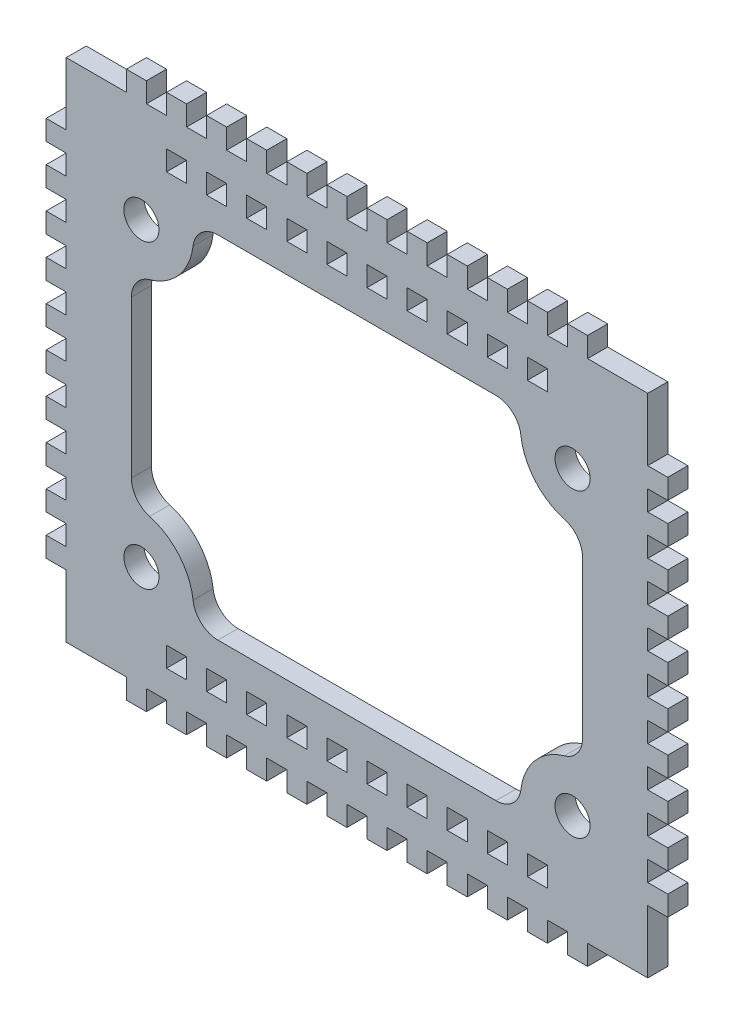
SolidWorks part; units mm, degrees
material "Cedar"
ref_plane "Front Plane" through (0, 0, 0) normal (0, 0, 1) x (1, 0, 0)
ref_plane "Top Plane" through (0, 0, 0) normal (0, 1, 0) x (1, 0, 0)
ref_plane "Right Plane" through (0, 0, 0) normal (1, 0, 0) x (0, 0, -1)
sketch "Sketch1" plane through (0, 0, 0) normal (0, 0, 1) x (1, 0, 0)
  line L0 (0, 0) -> (0, 50) construction
  line L1 (0, 0) -> (-64, 0) construction
  line L2 (-58, -50.5) -> (-58, 50.5)
  line L3 (-58, 50.5) -> (58, 50.5)
  line L4 (-45, -20) -> (-45, 20)
  line L5 (-33, 35) -> (33, 35)
  line L6 (45, -20) -> (45, 20)
  line L7 (58, -50.5) -> (58, 50.5)
  line L8 (-58, -50.5) -> (58, -50.5)
  line L9 (-33, -35) -> (33, -35)
  circle A0 centre (-43, 30) radius 3.5
  arc A1 (-45, 20) -> (-33, 35) centre (-44.6174, 31.9939) ccw
  arc A2 (45, -20) -> (33, -35) centre (44.6174, -31.9939) ccw
  circle A3 centre (43, 30) radius 3.5
  circle A4 centre (43, -30) radius 3.5
  circle A5 centre (-43, -30) radius 3.5
  arc A6 (45, 20) -> (33, 35) centre (44.6174, 31.9939) cw
  arc A7 (-45, -20) -> (-33, -35) centre (-44.6174, -31.9939) cw
  point P19 (0, 35)
  point P21 (0, 50.5)
  point P27 (-64, 0)
  point P28 (64, 0)
  point P29 (45, 0)
  point P34 (-45, 0)
  dimension "D3" = 7
  dimension "D8" = 50.5
  dimension "D7" = 10
  dimension "D9" = 35
  dimension "D10" = 12
  dimension "D11" = 50.5
  dimension "D1" = 10
  dimension "D2" = 116
  dimension "D4" = 43
  dimension "D5" = 45
  dimension "D6" = 30
extrude "Boss-Extrude1" add sketch "Sketch1" along normal blind 4
sketch "Sketch3" plane through (0, 0, 4) normal (0, 0, 1) x (1, 0, 0)
  line L0 (0, 0) -> (0, 54.6046) construction
  line L3 (-58, 50.5) -> (58, 50.5) construction
  line L6 (-14, 40.75) -> (-14, 44.75)
  line L7 (-10, 44.75) -> (-14, 44.75)
  line L8 (-10, 40.75) -> (-10, 44.75)
  line L9 (-10, 40.75) -> (-14, 40.75)
  line L10 (-22, 40.75) -> (-22, 44.75)
  line L12 (-18, 44.75) -> (-22, 44.75)
  line L13 (-18, 40.75) -> (-18, 44.75)
  line L14 (-18, 40.75) -> (-22, 40.75)
  line L15 (0, 0) -> (-26.3378, 0) construction
  line L16 (0, 0) -> (-64, 0) construction
  line L17 (-30, 40.75) -> (-30, 44.75)
  line L18 (-26, 44.75) -> (-30, 44.75)
  line L19 (-26, 40.75) -> (-26, 44.75)
  line L20 (-26, 40.75) -> (-30, 40.75)
  line L21 (33, -35) -> (33, -50.5) construction
  line L22 (-58, -50.5) -> (58, -50.5) construction
  line L24 (-14, -41) -> (-10, -41)
  line L25 (-6, -41) -> (-2, -41)
  line L26 (-6, -41) -> (-6, -45)
  line L27 (-6, -45) -> (-2, -45)
  line L28 (-2, -41) -> (-2, -45)
  line L29 (-38, 40.75) -> (-38, 44.75)
  line L30 (-34, 44.75) -> (-38, 44.75)
  line L31 (-34, 40.75) -> (-34, 44.75)
  line L32 (-34, 40.75) -> (-38, 40.75)
  line L33 (2, 40.75) -> (6, 40.75)
  line L35 (2, 40.75) -> (2, 44.75)
  line L36 (2, 44.75) -> (6, 44.75)
  line L37 (6, 40.75) -> (6, 44.75)
  line L39 (34, 40.75) -> (38, 40.75)
  line L40 (34, 40.75) -> (34, 44.75)
  line L41 (34, 44.75) -> (38, 44.75)
  line L42 (38, 40.75) -> (38, 44.75)
  line L43 (26, 40.75) -> (30, 40.75)
  line L44 (26, 40.75) -> (26, 44.75)
  line L45 (26, 44.75) -> (30, 44.75)
  line L46 (30, 40.75) -> (30, 44.75)
  line L47 (18, 40.75) -> (22, 40.75)
  line L48 (18, 40.75) -> (18, 44.75)
  line L49 (18, 44.75) -> (22, 44.75)
  line L50 (22, 40.75) -> (22, 44.75)
  line L51 (10, 40.75) -> (14, 40.75)
  line L52 (10, 40.75) -> (10, 44.75)
  line L53 (10, 44.75) -> (14, 44.75)
  line L54 (14, 40.75) -> (14, 44.75)
  line L55 (-14, -41) -> (-14, -45)
  line L56 (-14, -45) -> (-10, -45)
  line L57 (-10, -41) -> (-10, -45)
  line L58 (-6, 40.75) -> (-6, 44.75)
  line L59 (-2, 44.75) -> (-6, 44.75)
  line L60 (-2, 40.75) -> (-2, 44.75)
  line L61 (-2, 40.75) -> (-6, 40.75)
  line L62 (-22, -41) -> (-18, -41)
  line L63 (-22, -41) -> (-22, -45)
  line L64 (-22, -45) -> (-18, -45)
  line L65 (-18, -41) -> (-18, -45)
  line L66 (-30, -41) -> (-26, -41)
  line L67 (-30, -41) -> (-30, -45)
  line L68 (-30, -45) -> (-26, -45)
  line L69 (-26, -41) -> (-26, -45)
  line L70 (-38, -41) -> (-34, -41)
  line L71 (-38, -41) -> (-38, -45)
  line L72 (-38, -45) -> (-34, -45)
  line L73 (-34, -41) -> (-34, -45)
  line L74 (34, -41) -> (34, -45)
  line L75 (38, -45) -> (34, -45)
  line L76 (38, -41) -> (38, -45)
  line L77 (38, -41) -> (34, -41)
  line L78 (26, -41) -> (26, -45)
  line L79 (30, -45) -> (26, -45)
  line L80 (30, -41) -> (30, -45)
  line L81 (30, -41) -> (26, -41)
  line L82 (18, -41) -> (18, -45)
  line L83 (22, -45) -> (18, -45)
  line L84 (22, -41) -> (22, -45)
  line L85 (22, -41) -> (18, -41)
  line L86 (10, -41) -> (10, -45)
  line L87 (14, -45) -> (10, -45)
  line L88 (14, -41) -> (14, -45)
  line L89 (2, -41) -> (2, -45)
  line L90 (6, -45) -> (2, -45)
  line L91 (6, -41) -> (6, -45)
  line L92 (6, -41) -> (2, -41)
  line L93 (14, -41) -> (10, -41)
  dimension "D1" = 5.75
  dimension "D2" = 4
  dimension "D3" = 4
  dimension "D4" = 4
  dimension "D6" = 2
  dimension "D7" = 5
  dimension "D8" = 5.5
  dimension "D9" = 5
  dimension "D5" = 4
  dimension "D10" = 2
extrude "Cut-Extrude2" cut sketch "Sketch3" against normal blind 4
fillet "Fillet1" radius 5 1 edges at (-45, 20, 2)
fillet "Fillet2" radius 5 1 edges at (-33, 35, 2)
fillet "Fillet3" radius 5 1 edges at (33, 35, 2)
fillet "Fillet4" radius 5 1 edges at (45, 20, 2)
fillet "Fillet5" radius 5 1 edges at (33, -35, 2)
fillet "Fillet6" radius 5 1 edges at (45, -20, 2)
fillet "Fillet7" radius 5 1 edges at (-45, -20, 2)
fillet "Fillet8" radius 5 1 edges at (-33, -35, 2)
sketch "Sketch4" plane through (0, 0, 4) normal (0, 0, 1) x (1, 0, 0)
  line L0 (-58, -50.5) -> (-58, 50.5) construction
  line L1 (-58, 6) -> (-62, 6)
  line L2 (-58, 6) -> (-58, 2)
  line L3 (-58, 2) -> (-62, 2)
  line L4 (-62, 6) -> (-62, 2)
  line L5 (0, 0) -> (-64, 0) construction
  line L6 (-58, 14) -> (-62, 14)
  line L7 (-58, 14) -> (-58, 10)
  line L8 (-58, 10) -> (-62, 10)
  line L9 (-62, 14) -> (-62, 10)
  line L10 (-58, 22) -> (-62, 22)
  line L11 (-58, 22) -> (-58, 18)
  line L12 (-58, 18) -> (-62, 18)
  line L13 (-62, 22) -> (-62, 18)
  line L14 (-58, 30) -> (-62, 30)
  line L15 (-58, 30) -> (-58, 26)
  line L16 (-58, 26) -> (-62, 26)
  line L17 (-62, 30) -> (-62, 26)
  line L18 (-58, 38) -> (-62, 38)
  line L19 (-58, 38) -> (-58, 34)
  line L20 (-58, 34) -> (-62, 34)
  line L21 (-62, 38) -> (-62, 34)
  line L22 (0, 0) -> (-100.6812, 0) construction
  line L23 (-62, -38) -> (-62, -34)
  line L24 (-58, -34) -> (-62, -34)
  line L25 (-58, -38) -> (-58, -34)
  line L26 (-58, -38) -> (-62, -38)
  line L27 (-62, -30) -> (-62, -26)
  line L28 (-58, -26) -> (-62, -26)
  line L29 (-58, -30) -> (-58, -26)
  line L30 (-58, -30) -> (-62, -30)
  line L31 (-62, -22) -> (-62, -18)
  line L32 (-58, -18) -> (-62, -18)
  line L33 (-58, -22) -> (-58, -18)
  line L34 (-58, -22) -> (-62, -22)
  line L35 (-62, -14) -> (-62, -10)
  line L36 (-58, -10) -> (-62, -10)
  line L37 (-58, -14) -> (-58, -10)
  line L38 (-58, -14) -> (-62, -14)
  line L39 (-62, -6) -> (-62, -2)
  line L40 (-58, -2) -> (-62, -2)
  line L41 (-58, -6) -> (-58, -2)
  line L42 (-58, -6) -> (-62, -6)
  line L43 (0, 0) -> (0, 62.8153) construction
  line L44 (58, -6) -> (62, -6)
  line L45 (58, -6) -> (58, -2)
  line L46 (58, -2) -> (62, -2)
  line L47 (62, -6) -> (62, -2)
  line L48 (58, -14) -> (62, -14)
  line L49 (58, -14) -> (58, -10)
  line L50 (58, -10) -> (62, -10)
  line L51 (62, -14) -> (62, -10)
  line L52 (58, -22) -> (62, -22)
  line L53 (58, -22) -> (58, -18)
  line L54 (58, -18) -> (62, -18)
  line L55 (62, -22) -> (62, -18)
  line L56 (58, -30) -> (62, -30)
  line L57 (58, -30) -> (58, -26)
  line L58 (58, -26) -> (62, -26)
  line L59 (62, -30) -> (62, -26)
  line L60 (58, -38) -> (62, -38)
  line L61 (58, -38) -> (58, -34)
  line L62 (58, -34) -> (62, -34)
  line L63 (62, -38) -> (62, -34)
  line L64 (62, 38) -> (62, 34)
  line L65 (58, 34) -> (62, 34)
  line L66 (58, 38) -> (58, 34)
  line L67 (58, 38) -> (62, 38)
  line L68 (62, 30) -> (62, 26)
  line L69 (58, 26) -> (62, 26)
  line L70 (58, 30) -> (58, 26)
  line L71 (58, 30) -> (62, 30)
  line L72 (62, 22) -> (62, 18)
  line L73 (58, 18) -> (62, 18)
  line L74 (58, 22) -> (58, 18)
  line L75 (58, 22) -> (62, 22)
  line L76 (62, 14) -> (62, 10)
  line L77 (58, 10) -> (62, 10)
  line L78 (58, 14) -> (58, 10)
  line L79 (58, 14) -> (62, 14)
  line L80 (62, 6) -> (62, 2)
  line L81 (58, 2) -> (62, 2)
  line L82 (58, 6) -> (58, 2)
  line L83 (58, 6) -> (62, 6)
  dimension "D1" = 4
  dimension "D2" = 4
  dimension "D3" = 2
  dimension "D4" = 5
extrude "Boss-Extrude2" add sketch "Sketch4" against normal blind 4
sketch "Sketch5" plane through (0, 0, 0) normal (0, 0, -1) x (-1, 0, 0)
  line L0 (58, 50.5) -> (-58, 50.5) construction
  line L1 (-2, 50.5) -> (-6, 50.5)
  line L2 (-2, 50.5) -> (-2, 54.5)
  line L3 (-2, 54.5) -> (-6, 54.5)
  line L4 (-6, 50.5) -> (-6, 54.5)
  line L5 (0, 0) -> (0, 50) construction
  line L6 (-10, 50.5) -> (-14, 50.5)
  line L7 (-10, 50.5) -> (-10, 54.5)
  line L8 (-10, 54.5) -> (-14, 54.5)
  line L9 (-14, 50.5) -> (-14, 54.5)
  line L10 (-18, 50.5) -> (-22, 50.5)
  line L11 (-18, 50.5) -> (-18, 54.5)
  line L12 (-18, 54.5) -> (-22, 54.5)
  line L13 (-22, 50.5) -> (-22, 54.5)
  line L14 (-26, 50.5) -> (-30, 50.5)
  line L15 (-26, 50.5) -> (-26, 54.5)
  line L16 (-26, 54.5) -> (-30, 54.5)
  line L17 (-30, 50.5) -> (-30, 54.5)
  line L18 (-34, 50.5) -> (-38, 50.5)
  line L19 (-34, 50.5) -> (-34, 54.5)
  line L20 (-34, 54.5) -> (-38, 54.5)
  line L21 (-38, 50.5) -> (-38, 54.5)
  line L22 (-42, 50.5) -> (-46, 50.5)
  line L23 (-42, 50.5) -> (-42, 54.5)
  line L24 (-42, 54.5) -> (-46, 54.5)
  line L25 (-46, 50.5) -> (-46, 54.5)
  line L26 (0, 50) -> (0, 31.2256) construction
  line L27 (46, 50.5) -> (46, 54.5)
  line L28 (42, 54.5) -> (46, 54.5)
  line L29 (42, 50.5) -> (42, 54.5)
  line L30 (42, 50.5) -> (46, 50.5)
  line L31 (38, 50.5) -> (38, 54.5)
  line L32 (34, 54.5) -> (38, 54.5)
  line L33 (34, 50.5) -> (34, 54.5)
  line L34 (34, 50.5) -> (38, 50.5)
  line L35 (30, 50.5) -> (30, 54.5)
  line L36 (26, 54.5) -> (30, 54.5)
  line L37 (26, 50.5) -> (26, 54.5)
  line L38 (26, 50.5) -> (30, 50.5)
  line L39 (22, 50.5) -> (22, 54.5)
  line L40 (18, 54.5) -> (22, 54.5)
  line L41 (18, 50.5) -> (18, 54.5)
  line L42 (18, 50.5) -> (22, 50.5)
  line L43 (14, 50.5) -> (14, 54.5)
  line L44 (10, 54.5) -> (14, 54.5)
  line L45 (10, 50.5) -> (10, 54.5)
  line L46 (10, 50.5) -> (14, 50.5)
  line L47 (6, 50.5) -> (6, 54.5)
  line L48 (2, 54.5) -> (6, 54.5)
  line L49 (2, 50.5) -> (2, 54.5)
  line L50 (2, 50.5) -> (6, 50.5)
  line L51 (0, 0) -> (26, 0) construction
  line L52 (0, 0) -> (64, 0) construction
  line L53 (2, -50.5) -> (6, -50.5)
  line L54 (2, -50.5) -> (2, -54.5)
  line L55 (2, -54.5) -> (6, -54.5)
  line L56 (6, -50.5) -> (6, -54.5)
  line L57 (10, -50.5) -> (14, -50.5)
  line L58 (10, -50.5) -> (10, -54.5)
  line L59 (10, -54.5) -> (14, -54.5)
  line L60 (14, -50.5) -> (14, -54.5)
  line L61 (18, -50.5) -> (22, -50.5)
  line L62 (18, -50.5) -> (18, -54.5)
  line L63 (18, -54.5) -> (22, -54.5)
  line L64 (22, -50.5) -> (22, -54.5)
  line L65 (26, -50.5) -> (30, -50.5)
  line L66 (26, -50.5) -> (26, -54.5)
  line L67 (26, -54.5) -> (30, -54.5)
  line L68 (30, -50.5) -> (30, -54.5)
  line L69 (34, -50.5) -> (38, -50.5)
  line L70 (34, -50.5) -> (34, -54.5)
  line L71 (34, -54.5) -> (38, -54.5)
  line L72 (38, -50.5) -> (38, -54.5)
  line L73 (42, -50.5) -> (46, -50.5)
  line L74 (42, -50.5) -> (42, -54.5)
  line L75 (42, -54.5) -> (46, -54.5)
  line L76 (46, -50.5) -> (46, -54.5)
  line L77 (-46, -50.5) -> (-46, -54.5)
  line L78 (-42, -54.5) -> (-46, -54.5)
  line L79 (-42, -50.5) -> (-42, -54.5)
  line L80 (-42, -50.5) -> (-46, -50.5)
  line L81 (-38, -50.5) -> (-38, -54.5)
  line L82 (-34, -54.5) -> (-38, -54.5)
  line L83 (-34, -50.5) -> (-34, -54.5)
  line L84 (-34, -50.5) -> (-38, -50.5)
  line L85 (-30, -50.5) -> (-30, -54.5)
  line L86 (-26, -54.5) -> (-30, -54.5)
  line L87 (-26, -50.5) -> (-26, -54.5)
  line L88 (-26, -50.5) -> (-30, -50.5)
  line L89 (-22, -50.5) -> (-22, -54.5)
  line L90 (-18, -54.5) -> (-22, -54.5)
  line L91 (-18, -50.5) -> (-18, -54.5)
  line L92 (-18, -50.5) -> (-22, -50.5)
  line L93 (-14, -50.5) -> (-14, -54.5)
  line L94 (-10, -54.5) -> (-14, -54.5)
  line L95 (-10, -50.5) -> (-10, -54.5)
  line L96 (-10, -50.5) -> (-14, -50.5)
  line L97 (-6, -50.5) -> (-6, -54.5)
  line L98 (-2, -54.5) -> (-6, -54.5)
  line L99 (-2, -50.5) -> (-2, -54.5)
  line L100 (-2, -50.5) -> (-6, -50.5)
  dimension "D1" = 4
  dimension "D2" = 4
  dimension "D3" = 2
  dimension "D4" = 6
extrude "Boss-Extrude3" add sketch "Sketch5" against normal blind 4
